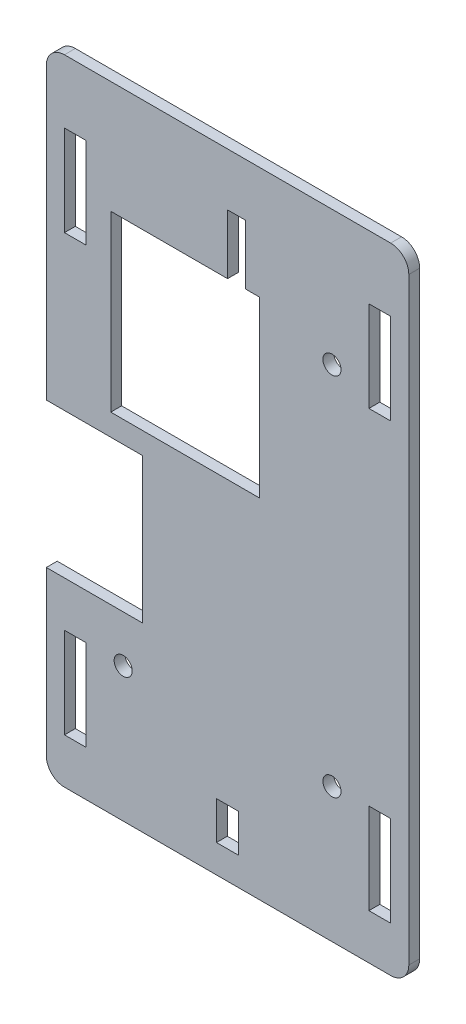
SolidWorks part; units mm, degrees
material "Pine"
ref_plane "Front Plane" through (0, 0, 0) normal (0, 0, 1) x (1, 0, 0)
ref_plane "Top Plane" through (0, 0, 0) normal (0, 1, 0) x (1, 0, 0)
ref_plane "Right Plane" through (0, 0, 0) normal (1, 0, 0) x (0, 0, -1)
sketch "Sketch1" plane through (0, 0, 0) normal (0, 0, 1) x (1, 0, 0)
  line L1 (-100, -175) -> (100, -175)
  line L2 (-100, -175) -> (-100, 175)
  line L3 (-100, 175) -> (100, 175)
  line L4 (100, -175) -> (100, 175)
  line L5 (-100, -175) -> (100, 175) construction
  line L6 (-100, 175) -> (100, -175) construction
  circle A0 centre (-57.5886, 100.78) radius 5
  circle A1 centre (57.5886, 100.78) radius 5
  circle A2 centre (57.5886, -100.78) radius 5
  circle A3 centre (-57.5886, -100.78) radius 5
  point P0 (0, 0)
  dimension "D3" = 10
  dimension "D1" = 350
  dimension "D2" = 200
  dimension "D4" = 74.22
extrude "Boss-Extrude1" add sketch "Sketch1" along normal blind 6
fillet "Fillet1" radius 10 4 edges at (-100, 175, 3) (100, 175, 3) (100, -175, 3) (-100, -175, 3)
sketch "Sketch2" plane through (0, 0, 6) normal (0, 0, 1) x (1, 0, 0)
  line L0 (10.0015, 113) -> (17.5515, 113)
  line L1 (-90, 140) -> (-78, 140)
  line L2 (-90, 140) -> (-90, 90)
  line L3 (-90, 90) -> (-78, 90)
  line L4 (-78, 140) -> (-78, 90)
  line L5 (-90, 140) -> (-78, 90) construction
  line L6 (-90, 90) -> (-78, 140) construction
  line L7 (-90, -100) -> (-78, -100)
  line L8 (-90, -100) -> (-90, -150)
  line L9 (-90, -150) -> (-78, -150)
  line L10 (-78, -100) -> (-78, -150)
  line L11 (-90, -100) -> (-78, -150) construction
  line L12 (-90, -150) -> (-78, -100) construction
  line L13 (90, -100) -> (78, -100)
  line L14 (90, -100) -> (90, -150)
  line L15 (90, -150) -> (78, -150)
  line L16 (78, -100) -> (78, -150)
  line L17 (90, -100) -> (78, -150) construction
  line L18 (90, -150) -> (78, -100) construction
  line L19 (78, 140) -> (90, 140)
  line L20 (78, 140) -> (78, 90)
  line L21 (78, 90) -> (90, 90)
  line L22 (90, 140) -> (90, 90)
  line L23 (78, 140) -> (90, 90) construction
  line L24 (78, 90) -> (90, 140) construction
  line L25 (-100, 165) -> (-100, -165) construction
  line L26 (90, 175) -> (-90, 175) construction
  line L27 (100, -165) -> (100, 165) construction
  line L28 (-90, -175) -> (90, -175) construction
  line L29 (-64.4485, 113) -> (0.0015, 113)
  line L30 (-64.4485, 113) -> (-64.4485, 17)
  line L31 (-64.4485, 17) -> (17.5515, 17)
  line L32 (17.5515, 113) -> (17.5515, 17)
  line L33 (-64.4485, 113) -> (17.5515, 17) construction
  line L34 (-64.4485, 17) -> (17.5515, 113) construction
  line L35 (0.0015, 145.8802) -> (10.0015, 145.8802)
  line L36 (0.0015, 145.8802) -> (0.0015, 113)
  line L38 (10.0015, 145.8802) -> (10.0015, 113)
  line L39 (0.0015, 145.8802) -> (10.0015, 113) construction
  line L40 (0.0015, 113) -> (10.0015, 145.8802) construction
  line L41 (-101, 5) -> (-47, 5)
  line L42 (-101, 5) -> (-101, -75)
  line L43 (-101, -75) -> (-47, -75)
  line L44 (-47, 5) -> (-47, -75)
  line L45 (-101, 5) -> (-47, -75) construction
  line L46 (-101, -75) -> (-47, 5) construction
  line L47 (-6.125, -138.5) -> (6.125, -138.5)
  line L48 (-6.125, -138.5) -> (-6.125, -159.5)
  line L49 (-6.125, -159.5) -> (6.125, -159.5)
  line L50 (6.125, -138.5) -> (6.125, -159.5)
  line L51 (-6.125, -138.5) -> (6.125, -159.5) construction
  line L52 (-6.125, -159.5) -> (6.125, -138.5) construction
  point P0 (-84, 115)
  point P5 (-84, -125)
  point P10 (84, -125)
  point P15 (84, 115)
  point P26 (-23.4485, 65)
  point P33 (5.0015, 129.4401)
  point P38 (-74, -35)
  point P43 (0, -149)
  dimension "D14" = 54
  dimension "D16" = 26
  dimension "D17" = 100
  dimension "D1" = 12
  dimension "D2" = 60
  dimension "D3" = 10
  dimension "D4" = 240
  dimension "D5" = 10
  dimension "D6" = 50
  dimension "D7" = 240
  dimension "D8" = 96
  dimension "D9" = 82
  dimension "D10" = 35.5515
  dimension "D11" = 16.4401
  dimension "D12" = 10
  dimension "D13" = 7.55
  dimension "D15" = 80
  dimension "D18" = 12.25
  dimension "D19" = 21
  dimension "D20" = 26
  dimension "D21" = 100
extrude "Cut-Extrude1" cut sketch "Sketch2" against normal through all
